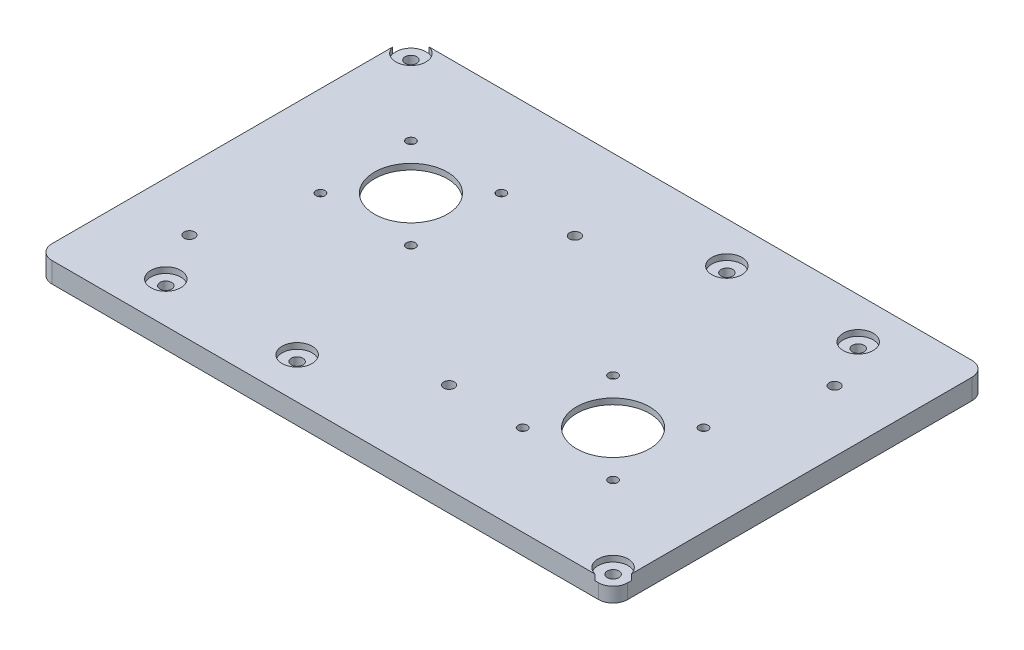
SolidWorks part; units mm, degrees
ref_plane "Front Plane" through (0, 0, 0) normal (0, 0, 1) x (1, 0, 0)
ref_plane "Top Plane" through (0, 0, 0) normal (0, 1, 0) x (1, 0, 0)
ref_plane "Right Plane" through (0, 0, 0) normal (1, 0, 0) x (0, 0, -1)
sketch "Sketch1" plane through (0, 0, 0) normal (0, 1, 0) x (1, 0, 0)
  line L0 (-112.6514, -4.5784) -> (-69.6514, 38.4216) construction
  line L1 (-132.6514, 63.4216) -> (54.6318, 63.4216)
  line L2 (-137.6514, 58.4216) -> (-137.6514, -59.5784)
  line L3 (-132.6514, -64.5784) -> (54.6318, -64.5784)
  line L4 (59.6318, 58.4216) -> (59.6318, -59.5784)
  line L5 (-112.6514, 38.4216) -> (-69.6514, 38.4216)
  line L6 (-112.6514, 38.4216) -> (-112.6514, -4.5784)
  line L7 (-112.6514, -4.5784) -> (-69.6514, -4.5784)
  line L8 (-69.6514, 38.4216) -> (-69.6514, -4.5784)
  line L9 (-8.3682, 3.4216) -> (34.6318, 3.4216)
  line L10 (-8.3682, 3.4216) -> (-8.3682, -39.5784)
  line L11 (-8.3682, -39.5784) -> (34.6318, -39.5784)
  line L12 (34.6318, 3.4216) -> (34.6318, -39.5784)
  line L13 (-91.1514, 66.9216) -> (105.133, 66.9216) construction
  line L14 (-8.3682, -39.5784) -> (34.6318, 3.4216) construction
  line L15 (13.1318, 31.9216) -> (105.133, 31.9216) construction
  line L16 (-91.1514, -33.0784) -> (-225.2939, -33.0784) construction
  circle A2 centre (-91.1514, 16.9216) radius 50 construction
  circle A3 centre (13.1318, -18.0784) radius 50 construction
  circle A4 centre (-132.6514, 58.4216) radius 5 construction
  circle A5 centre (-132.6514, 58.4216) radius 2
  arc A6 (59.6318, 58.4216) -> (54.6318, 63.4216) centre (54.6318, 58.4216) ccw
  arc A7 (59.6318, -59.5784) -> (54.6318, -64.5784) centre (54.6318, -59.5784) cw
  arc A8 (-137.6514, -59.5784) -> (-132.6514, -64.5784) centre (-132.6514, -59.5784) ccw
  arc A9 (-137.6514, 58.4216) -> (-132.6514, 63.4216) centre (-132.6514, 58.4216) cw
  circle A10 centre (54.6318, -59.5784) radius 5 construction
  circle A11 centre (54.6318, -59.5784) radius 2
  circle A12 centre (-15.3682, 49.4216) radius 5 construction
  circle A13 centre (29.6318, 49.4216) radius 2
  circle A14 centre (-15.3682, 49.4216) radius 2
  circle A15 centre (29.6318, 49.4216) radius 5 construction
  circle A16 centre (-107.6514, -50.5784) radius 2
  circle A17 centre (-62.6514, -50.5784) radius 5 construction
  circle A18 centre (-62.6514, -50.5784) radius 2
  circle A19 centre (-107.6514, -50.5784) radius 5 construction
  point P12 (13.1318, -18.0784)
  point P13 (-91.1514, 16.9216)
  dimension "D8" = 100
  dimension "D9" = 10
  dimension "D10" = 4
  dimension "D13" = 5
  dimension "D14" = 4
  dimension "D15" = 10
  dimension "D16" = 4
  dimension "D1" = 25
  dimension "D2" = 25
  dimension "D3" = 43
  dimension "D4" = 35
  dimension "D5" = 110
  dimension "D6" = 25
  dimension "D7" = 25
  dimension "D11" = 5
  dimension "D12" = 5
  dimension "D17" = 45
  dimension "D18" = 14
  dimension "D19" = 45
  dimension "D20" = 14
  dimension "D21" = 30
  dimension "D22" = 30
extrude "Boss-Extrude1" add sketch "Sketch1" along normal blind 7
sketch "Sketch2" plane through (0, 7, 0) normal (0, 1, 0) x (1, 0, 0)
  line L0 (-69.6514, 38.4216) -> (-69.6514, -4.5784) construction
  line L1 (-112.6514, 38.4216) -> (-69.6514, 38.4216)
  line L2 (-112.6514, 38.4216) -> (-112.6514, -4.5784)
  line L3 (-112.6514, -4.5784) -> (-69.6514, -4.5784)
  line L4 (-69.6514, 38.4216) -> (-69.6514, -4.5784)
  line L5 (-112.6514, -4.5784) -> (-69.6514, -4.5784) construction
  line L6 (-112.6514, 38.4216) -> (-69.6514, -4.5784) construction
  line L7 (-112.6514, -4.5784) -> (-69.6514, 38.4216) construction
  line L8 (-69.6514, 38.4216) -> (-112.6514, 38.4216)
  line L9 (-69.6514, 38.4216) -> (-69.6514, -4.5784)
  line L10 (-69.6514, -4.5784) -> (-112.6514, -4.5784)
  line L11 (-112.6514, 38.4216) -> (-112.6514, -4.5784)
  line L12 (-69.6514, -4.5784) -> (-69.6514, 38.4216)
  line L13 (-69.6514, -4.5784) -> (-112.6514, -4.5784)
  line L14 (-112.6514, -4.5784) -> (-112.6514, 38.4216)
  line L15 (-69.6514, 38.4216) -> (-112.6514, 38.4216)
  line L16 (-112.6514, -4.5784) -> (-69.6514, -4.5784)
  line L17 (-112.6514, -4.5784) -> (-112.6514, 38.4216)
  line L18 (-112.6514, 38.4216) -> (-69.6514, 38.4216)
  line L19 (-69.6514, -4.5784) -> (-69.6514, 38.4216)
  line L28 (-136.187, -63.114) -> (58.1674, 61.9571) construction
  line L29 (34.6318, -39.5784) -> (-8.3682, -39.5784)
  line L30 (34.6318, -39.5784) -> (34.6318, 3.4216)
  line L31 (34.6318, 3.4216) -> (-8.3682, 3.4216)
  line L32 (-8.3682, -39.5784) -> (-8.3682, 3.4216)
  line L33 (-8.3682, -39.5784) -> (34.6318, -39.5784)
  line L34 (-8.3682, -39.5784) -> (-8.3682, 3.4216)
  line L35 (-8.3682, 3.4216) -> (34.6318, 3.4216)
  line L36 (34.6318, -39.5784) -> (34.6318, 3.4216)
  line L37 (-8.3682, 3.4216) -> (-8.3682, -39.5784)
  line L38 (-8.3682, 3.4216) -> (34.6318, 3.4216)
  line L39 (34.6318, 3.4216) -> (34.6318, -39.5784)
  line L40 (-8.3682, -39.5784) -> (34.6318, -39.5784)
  line L41 (34.6318, 3.4216) -> (-8.3682, 3.4216)
  line L42 (34.6318, 3.4216) -> (34.6318, -39.5784)
  line L43 (34.6318, -39.5784) -> (-8.3682, -39.5784)
  line L44 (-8.3682, 3.4216) -> (-8.3682, -39.5784)
  line L45 (34.6318, -39.5784) -> (-8.3682, 3.4216) construction
  line L46 (34.6318, 3.4216) -> (-8.3682, -39.5784) construction
  circle A0 centre (-91.1514, 16.9216) radius 12.5
  circle A1 centre (-106.6514, 32.4216) radius 1.55
  circle A3 centre (-75.6514, 32.4216) radius 1.55
  circle A4 centre (-91.1514, 16.9216) radius 12.5
  circle A5 centre (-75.6514, 1.4216) radius 1.55
  circle A6 centre (-91.1514, 16.9216) radius 12.5
  circle A7 centre (-106.6514, 1.4216) radius 1.55
  circle A8 centre (-91.1514, 16.9216) radius 12.5
  arc A22 (-137.6514, -59.5784) -> (-132.6514, -64.5784) centre (-132.6514, -59.5784) ccw construction
  arc A23 (59.6318, 58.4216) -> (54.6318, 63.4216) centre (54.6318, 58.4216) ccw construction
  circle A24 centre (13.1318, -18.0784) radius 12.5
  circle A25 centre (28.6318, -33.5784) radius 1.55
  circle A26 centre (-2.3682, -33.5784) radius 1.55
  circle A27 centre (13.1318, -18.0784) radius 12.5
  circle A28 centre (-2.3682, -2.5784) radius 1.55
  circle A29 centre (13.1318, -18.0784) radius 12.5
  circle A30 centre (28.6318, -2.5784) radius 1.55
  circle A31 centre (13.1318, -18.0784) radius 12.5
  point P37 (-91.1514, 16.9216)
  point P75 (13.1318, -18.0784)
  point P76 (-39.0098, -0.5784)
  dimension "D3" = 25
  dimension "D4" = 3.1
  dimension "D1" = 31
  dimension "D5" = 2
  dimension "D2" = 4
extrude "Boss-Extrude2" add sketch "Sketch2" against normal blind 2
sketch "Sketch3" plane through (0, 0, 0) normal (0, -1, 0) x (1, 0, 0)
  line L0 (-12.3682, 43.5784) -> (-12.3682, -7.4216)
  line L1 (-8.3682, 39.5784) -> (34.6318, 39.5784)
  line L2 (-8.3682, 39.5784) -> (-8.3682, -3.4216)
  line L3 (-8.3682, -3.4216) -> (34.6318, -3.4216)
  line L4 (34.6318, 39.5784) -> (34.6318, -3.4216)
  line L5 (-12.3682, -7.4216) -> (38.6318, -7.4216)
  line L6 (38.6318, 43.5784) -> (38.6318, -7.4216)
  line L7 (-12.3682, 43.5784) -> (38.6318, 43.5784)
  line L9 (-112.6514, -38.4216) -> (-69.6514, -38.4216)
  line L10 (-112.6514, -38.4216) -> (-112.6514, 4.5784)
  line L11 (-112.6514, 4.5784) -> (-69.6514, 4.5784)
  line L12 (-69.6514, -38.4216) -> (-69.6514, 4.5784)
  line L13 (-116.6514, 8.5784) -> (-65.6514, 8.5784)
  line L14 (-65.6514, -42.4216) -> (-65.6514, 8.5784)
  line L15 (-116.6514, -42.4216) -> (-65.6514, -42.4216)
  line L16 (-116.6514, -42.4216) -> (-116.6514, 8.5784)
  dimension "D1" = 4
  dimension "D2" = 4
extrude "Boss-Extrude3" add sketch "Sketch3" along normal blind 4
sketch "Sketch4" plane through (0, 7, 0) normal (0, 1, 0) x (1, 0, 0)
  circle A0 centre (-132.6514, 58.4216) radius 5.15
  circle A1 centre (-15.3682, 49.4216) radius 5.15
  circle A2 centre (29.6318, 49.4216) radius 5.15
  circle A3 centre (54.6318, -59.5784) radius 5.15
  circle A4 centre (-62.6514, -50.5784) radius 5.15
  circle A5 centre (-107.6514, -50.5784) radius 5.15
  dimension "D1" = 10.3
extrude "Cut-Extrude1" cut sketch "Sketch4" against normal blind 2
sketch "Sketch5" plane through (0, 0, 0) normal (0, -1, 0) x (1, 0, 0)
  line L0 (-116.6514, 33.494) -> (-27.6514, 33.494) construction
  line L1 (-137.6514, -58.4216) -> (-137.6514, 59.5784) construction
  line L2 (59.6318, 0.5784) -> (-137.6514, 0.5784) construction
  line L3 (59.6318, -58.4216) -> (59.6318, 59.5784) construction
  circle A0 centre (-116.6514, 33.494) radius 1.85
  circle A1 centre (-27.6514, 33.494) radius 1.85
  circle A2 centre (-50.3682, -32.3371) radius 1.85
  circle A3 centre (38.6318, -32.3371) radius 1.85
  point P10 (-39.0098, 0.5784)
  point P18 (-39.0098, 0.5784)
  dimension "D1" = 3.7
  dimension "D2" = 89
  dimension "D3" = 21
  dimension "D4" = 2
extrude "Cut-Extrude2" cut sketch "Sketch5" against normal blind 10
equation "\"D1@Sketch1\"=\"D2@Sketch1\""
equation "\"D6@Sketch1\"=\"D2@Sketch1\""
equation "\"D7@Sketch1\"=\"D2@Sketch1\""
equation "\"D19@Sketch1\"=\"D17@Sketch1\""
equation "\"D20@Sketch1\"=\"D18@Sketch1\""
